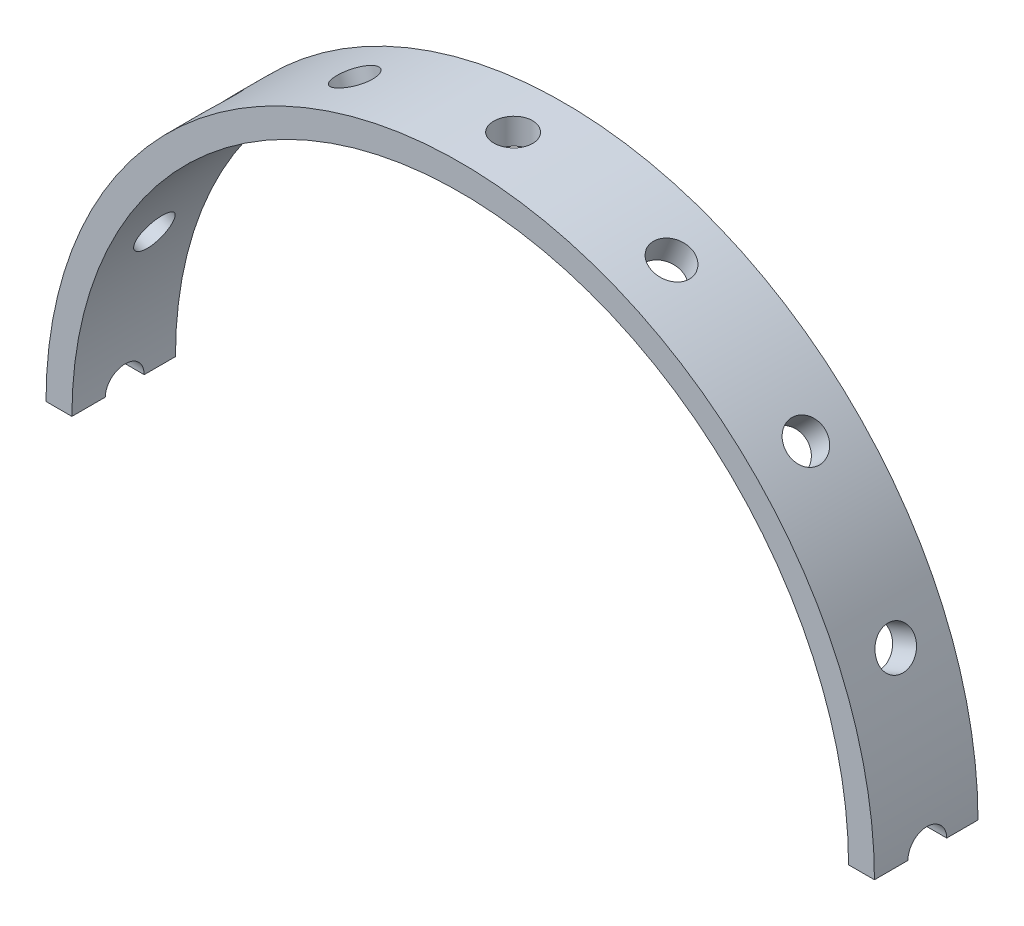
SolidWorks part; units mm, degrees
ref_plane "正面" through (0, 0, 0) normal (0, 0, 1) x (1, 0, 0)
ref_plane "平面" through (0, 0, 0) normal (0, 1, 0) x (1, 0, 0)
ref_plane "右側面" through (0, 0, 0) normal (1, 0, 0) x (0, 0, -1)
sketch "ｽｹｯﾁ1" plane through (0, 0, 0) normal (0, 0, 1) x (1, 0, 0)
  circle A0 centre (0, 0) radius 15
  circle A1 centre (0, 0) radius 16
  dimension "D1" = 30
  dimension "D2" = 32
extrude "ﾎﾞｽ - 押し出し1" add sketch "ｽｹｯﾁ1" along normal blind 4
sketch "ｽｹｯﾁ2" plane through (0, 0, 0) normal (0, 1, 0) x (1, 0, 0)
  circle A0 centre (0, -1.9576) radius 0.75
  dimension "D1" = 1.5
extrude "ｶｯﾄ - 押し出し1" cut sketch "ｽｹｯﾁ2" against normal through all
pattern_circular "円形ﾊﾟﾀｰﾝ1" count 16 over 360 about axis through (0, 0, 0) along (0, 0, 1) of "ｶｯﾄ - 押し出し1"
sketch "ｽｹｯﾁ3" plane through (0, 0, 0) normal (0, 1, 0) x (1, 0, 0)
  line L1 (18.3993, -8.0013) -> (-18.3993, -8.0013)
  line L2 (18.3993, -8.0013) -> (18.3993, 3.9448)
  line L3 (18.3993, 3.9448) -> (-18.3993, 3.9448)
  line L4 (-18.3993, -8.0013) -> (-18.3993, 3.9448)
  line L5 (18.3993, -8.0013) -> (-18.3993, 3.9448) construction
  line L6 (18.3993, 3.9448) -> (-18.3993, -8.0013) construction
  point P0 (0, -2.0282)
extrude "ｶｯﾄ - 押し出し2" cut sketch "ｽｹｯﾁ3" against normal through all
